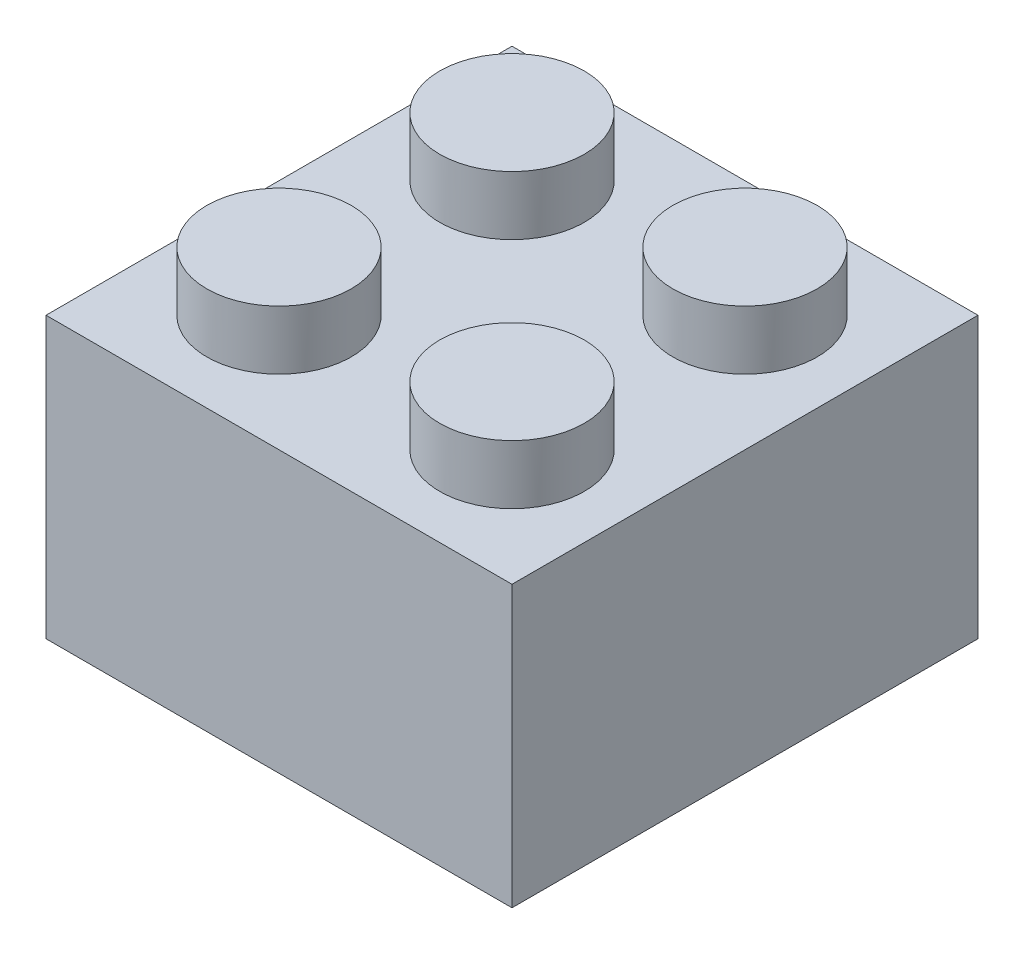
SolidWorks part; units mm, degrees
ref_plane "Front Plane" through (0, 0, 0) normal (0, 0, 1) x (1, 0, 0)
ref_plane "Top Plane" through (0, 0, 0) normal (0, 1, 0) x (1, 0, 0)
ref_plane "Right Plane" through (0, 0, 0) normal (1, 0, 0) x (0, 0, -1)
sketch "stencil" plane through (0, 0, 0) normal (0, 1, 0) x (1, 0, 0)
  line L2 (0, 0) -> (0, 3.95) construction
  line L29 (0, 0) -> (3.95, 0) construction
  line L30 (3.95, 0) -> (3.95, 3.95) construction
  line L31 (7.9, 0) -> (7.9, 3.95) construction
  line L32 (11.85, 0) -> (11.85, 3.95) construction
  line L36 (3.95, 3.95) -> (3.95, 7.9) construction
  line L37 (7.9, 3.95) -> (7.9, 7.9) construction
  line L38 (11.85, 3.95) -> (11.85, 7.9) construction
  line L39 (3.95, 7.9) -> (3.95, 11.85) construction
  line L40 (7.9, 7.9) -> (7.9, 11.85) construction
  line L41 (11.85, 7.9) -> (11.85, 11.85) construction
  line L52 (3.95, 11.85) -> (3.95, 15.8) construction
  line L53 (7.9, 11.85) -> (7.9, 15.8) construction
  line L55 (11.85, 11.85) -> (11.85, 15.8) construction
  line L56 (0, 3.95) -> (0, 7.9) construction
  line L57 (0, 7.9) -> (0, 11.85) construction
  line L58 (0, 11.85) -> (0, 15.8) construction
  line L59 (3.95, 0) -> (7.9, 0) construction
  line L60 (7.9, 0) -> (11.85, 0) construction
  line L61 (11.85, 0) -> (15.8, 0) construction
  line L62 (3.95, 3.95) -> (7.9, 3.95) construction
  line L63 (7.9, 3.95) -> (11.85, 3.95) construction
  line L64 (11.85, 3.95) -> (15.8, 3.95) construction
  line L65 (3.95, 7.9) -> (7.9, 7.9) construction
  line L66 (7.9, 7.9) -> (11.85, 7.9) construction
  line L67 (11.85, 7.9) -> (15.8, 7.9) construction
  line L68 (3.95, 11.85) -> (7.9, 11.85) construction
  line L69 (7.9, 11.85) -> (11.85, 11.85) construction
  line L70 (11.85, 11.85) -> (15.8, 11.85) construction
  line L71 (0, 3.95) -> (3.95, 3.95) construction
  line L72 (0, 7.9) -> (3.95, 7.9) construction
  line L73 (0, 11.85) -> (3.95, 11.85) construction
  line L74 (14.3, 14.3) -> (1.5, 14.3)
  line L75 (15.8, 15.8) -> (0, 15.8)
  line L76 (15.8, 15.8) -> (15.8, 0)
  line L77 (15.8, 0) -> (0, 0)
  line L78 (0, 15.8) -> (0, 0)
  line L79 (7.9, 0) -> (7.9, 15.8) construction
  line L80 (15.8, 7.9) -> (0, 7.9) construction
  line L81 (1.5, 14.3) -> (1.5, 1.5)
  line L82 (14.3, 1.5) -> (1.5, 1.5)
  line L83 (14.3, 14.3) -> (14.3, 1.5)
  circle A40 centre (7.9, 7.9) radius 3.25
  circle A41 centre (7.9, 7.9) radius 2.45
  circle A42 centre (3.95, 3.95) radius 2.45
  circle A43 centre (11.85, 3.95) radius 2.45
  circle A44 centre (11.85, 11.85) radius 2.45
  circle A45 centre (3.95, 11.85) radius 2.45
  point P6 (3.95, -15.8)
  point P9 (7.9, -15.8)
  point P10 (7.9, -11.85)
  point P13 (3.95, -7.9)
  point P15 (7.9, -7.9)
  point P17 (7.9, -3.95)
  point P18 (3.95, 0)
  point P21 (7.9, 0)
  point P25 (7.9, 3.95)
  point P27 (3.95, 7.9)
  point P28 (7.9, 7.9)
  point P29 (0, -11.85)
  point P30 (0, -7.9)
  point P31 (0, 3.95)
  point P34 (0, -3.95)
  point P36 (0, 15.8)
  point P37 (0, 23.7)
  point P38 (7.9, 23.7)
  point P39 (15.8, 23.7)
  point P40 (15.8, 15.8)
  point P41 (15.8, 7.9)
  dimension "D9" = 6.5
  dimension "D11" = 4.9
  dimension "D1" = 3.95
  dimension "D2" = 3.95
  dimension "D3" = 15.8
  dimension "D8" = 15.8
  dimension "D10" = 0.8
  dimension "D12" = 1.5
  dimension "D4" = 4
  dimension "D5" = 4
  dimension "D6" = 4
  dimension "D7" = 4
sketch "Sketch1" plane through (0, 0, 0) normal (0, 1, 0) x (1, 0, 0)
  line L5 (0, 0) -> (15.8, 0)
  line L6 (0, 0) -> (0, 15.8)
  line L7 (0, 15.8) -> (15.8, 15.8)
  line L8 (15.8, 0) -> (15.8, 15.8)
extrude "Boss-Extrude1" add sketch "Sketch1" along normal mid plane 9.5
sketch "Sketch2" plane through (0, 4.75, 0) normal (0, 1, 0) x (1, 0, 0)
  circle A9 centre (3.95, 3.95) radius 2.45
  circle A10 centre (3.95, 3.95) radius 2.45 construction
  circle A11 centre (11.85, 3.95) radius 2.45
  circle A12 centre (11.85, 11.85) radius 2.45
  circle A13 centre (3.95, 11.85) radius 2.45
extrude "Boss-Extrude2" add sketch "Sketch2" along normal blind 2
sketch "Sketch4" plane through (0, -4.75, 0) normal (0, -1, 0) x (1, 0, 0)
  line L6 (1.5, -1.5) -> (14.3, -1.5)
  line L8 (1.5, -1.5) -> (1.5, -14.3)
  line L9 (1.5, -14.3) -> (14.3, -14.3)
  line L10 (14.3, -1.5) -> (14.3, -14.3)
extrude "Cut-Extrude1" cut sketch "Sketch4" against normal blind 4
sketch "Sketch5" plane through (0, -0.75, 0) normal (0, -1, 0) x (1, 0, 0)
  circle A8 centre (7.9, -7.9) radius 3.25
  circle A9 centre (7.9, -7.9) radius 2.45
  circle A10 centre (7.9, -7.9) radius 3.25 construction
  circle A11 centre (7.9, -7.9) radius 2.45 construction
extrude "Boss-Extrude3" add sketch "Sketch5" along normal up to surface (4 mm away) up to face at (7.9, -4.75, -7.9)
sketch "Sketch7" plane through (0, -0.75, 0) normal (0, -1, 0) x (1, 0, 0)
  line L0 (3.95, -11.85) -> (3.95, -15.8) construction
  line L1 (0, -11.85) -> (3.95, -11.85) construction
  line L2 (0, -3.95) -> (3.95, -3.95) construction
  line L3 (3.95, 0) -> (3.95, -3.95) construction
  line L4 (11.85, 0) -> (11.85, -3.95) construction
  line L5 (11.85, -3.95) -> (15.8, -3.95) construction
  line L6 (11.85, -11.85) -> (15.8, -11.85) construction
  line L7 (11.85, -11.85) -> (11.85, -15.8) construction
  line L8 (14.3, -14.3) -> (1.5, -14.3) construction
  line L9 (1.5, -14.3) -> (1.5, -1.5) construction
  line L10 (14.3, -1.5) -> (1.5, -1.5) construction
  line L11 (14.3, -14.3) -> (14.3, -1.5) construction
  circle A0 centre (3.95, -14.3) radius 0.25
  circle A1 centre (1.5, -11.85) radius 0.25
  circle A2 centre (1.5, -3.95) radius 0.25
  circle A3 centre (3.95, -1.5) radius 0.25
  circle A4 centre (11.85, -1.5) radius 0.25
  circle A5 centre (14.3, -3.95) radius 0.25
  circle A6 centre (14.3, -11.85) radius 0.25
  circle A7 centre (11.85, -14.3) radius 0.25
  dimension "D1" = 0.5
extrude "Boss-Extrude4" add sketch "Sketch7" along normal up to surface (4 mm away) up to face at (7.9, -4.75, -7.9)
equation "\"t\"= 0.0'tolerance"
equation "\"D3@stencil\"=15.8-\"t\""
equation "\"D8@stencil\"=15.8-\"t\""
equation "\"D12@stencil\"=1.50-\"t\""
